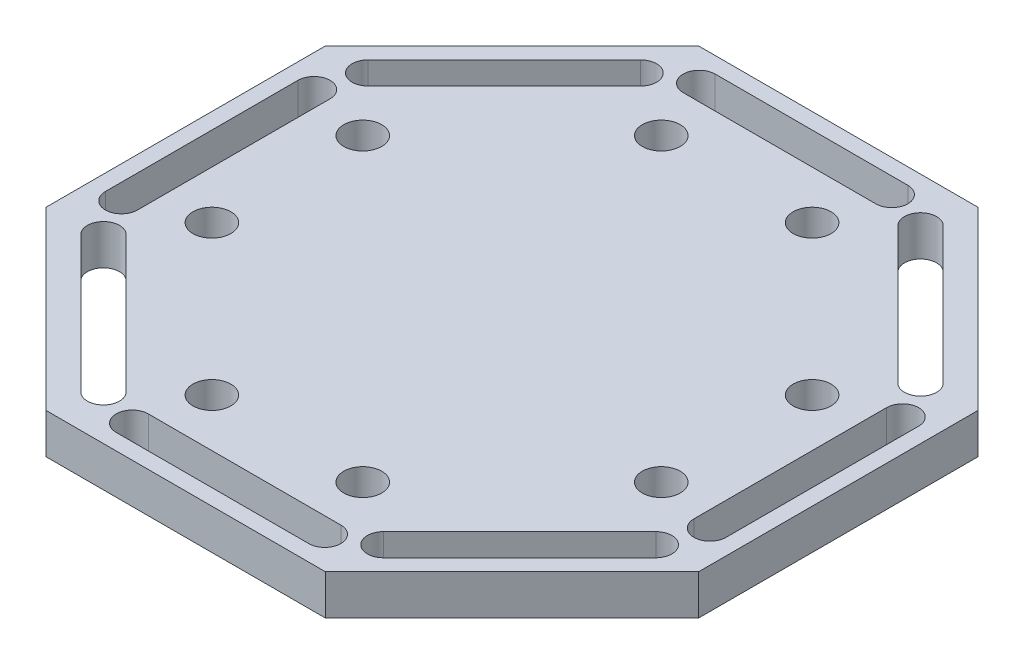
SolidWorks part; units mm, degrees
ref_plane "Front Plane" through (0, 0, 0) normal (0, 0, 1) x (1, 0, 0)
ref_plane "Top Plane" through (0, 0, 0) normal (0, 1, 0) x (1, 0, 0)
ref_plane "Right Plane" through (0, 0, 0) normal (1, 0, 0) x (0, 0, -1)
sketch "Sketch1" plane through (0, 0, 0) normal (0, 1, 0) x (1, 0, 0)
  line L0 (-22.86, -8.0471) -> (-22.86, 7.1929) construction
  line L2 (-25.4, 10.6219) -> (-25.4, -11.4761)
  line L4 (25.4, 11.4761) -> (25.4, -10.6219)
  line L5 (-25.4, 10.6219) -> (25.4, -10.6219) construction
  line L6 (-25.4, -11.4761) -> (25.4, 11.4761) construction
  line L7 (10.6219, -25.4) -> (-11.4761, -25.4)
  line L9 (11.4761, 25.4) -> (-10.6219, 25.4)
  line L11 (10.6219, -25.4) -> (-10.6219, 25.4) construction
  line L12 (11.4761, 25.4) -> (-11.4761, -25.4) construction
  line L13 (-24.13, -8.0471) -> (-24.13, 7.1929)
  line L14 (-25.4, 10.6219) -> (-10.6219, 25.4)
  line L15 (11.4761, 25.4) -> (25.4, 11.4761)
  line L16 (25.4, -10.6219) -> (10.6219, -25.4)
  line L17 (-11.4761, -25.4) -> (-25.4, -11.4761)
  line L18 (-21.59, -8.0471) -> (-21.59, 7.1929)
  line L19 (-20.9566, 9.5763) -> (-10.1803, 20.3526)
  line L20 (-22.7527, 11.3723) -> (-11.9763, 22.1486)
  line L21 (-21.8546, 10.4743) -> (-11.0783, 21.2506) construction
  line L22 (-8.0471, 21.59) -> (7.1929, 21.59)
  line L23 (-8.0471, 24.13) -> (7.1929, 24.13)
  line L24 (-8.0471, 22.86) -> (7.1929, 22.86) construction
  line L25 (9.5763, 20.9566) -> (20.3526, 10.1803)
  line L26 (11.3723, 22.7527) -> (22.1486, 11.9763)
  line L27 (10.4743, 21.8546) -> (21.2506, 11.0783) construction
  line L28 (21.59, 8.0471) -> (21.59, -7.1929)
  line L29 (24.13, 8.0471) -> (24.13, -7.1929)
  line L30 (22.86, 8.0471) -> (22.86, -7.1929) construction
  line L31 (20.9566, -9.5763) -> (10.1803, -20.3526)
  line L32 (22.7527, -11.3723) -> (11.9763, -22.1486)
  line L33 (21.8546, -10.4743) -> (11.0783, -21.2506) construction
  line L34 (8.0471, -21.59) -> (-7.1929, -21.59)
  line L35 (8.0471, -24.13) -> (-7.1929, -24.13)
  line L36 (8.0471, -22.86) -> (-7.1929, -22.86) construction
  line L37 (-9.5763, -20.9566) -> (-20.3526, -10.1803)
  line L38 (-11.3723, -22.7527) -> (-22.1486, -11.9763)
  line L39 (-10.4743, -21.8546) -> (-21.2506, -11.0783) construction
  circle A0 centre (-17.78, 5.969) radius 1.5
  circle A1 centre (-17.78, -5.969) radius 1.5
  circle A2 centre (-5.969, 17.78) radius 1.5
  circle A3 centre (5.969, 17.78) radius 1.5
  circle A4 centre (17.78, 5.969) radius 1.5
  circle A5 centre (17.78, -5.969) radius 1.5
  circle A6 centre (5.969, -17.78) radius 1.5
  circle A7 centre (-5.969, -17.78) radius 1.5
  arc A8 (-24.13, -8.0471) -> (-21.59, -8.0471) centre (-22.86, -8.0471) ccw
  arc A9 (-21.59, 7.1929) -> (-24.13, 7.1929) centre (-22.86, 7.1929) ccw
  arc A10 (-22.7527, 11.3723) -> (-20.9566, 9.5763) centre (-21.8546, 10.4743) ccw
  arc A11 (-10.1803, 20.3526) -> (-11.9763, 22.1486) centre (-11.0783, 21.2506) ccw
  arc A12 (-8.0471, 24.13) -> (-8.0471, 21.59) centre (-8.0471, 22.86) ccw
  arc A13 (7.1929, 21.59) -> (7.1929, 24.13) centre (7.1929, 22.86) ccw
  arc A14 (11.3723, 22.7527) -> (9.5763, 20.9566) centre (10.4743, 21.8546) ccw
  arc A15 (20.3526, 10.1803) -> (22.1486, 11.9763) centre (21.2506, 11.0783) ccw
  arc A16 (24.13, 8.0471) -> (21.59, 8.0471) centre (22.86, 8.0471) ccw
  arc A17 (21.59, -7.1929) -> (24.13, -7.1929) centre (22.86, -7.1929) ccw
  arc A18 (22.7527, -11.3723) -> (20.9566, -9.5763) centre (21.8546, -10.4743) ccw
  arc A19 (10.1803, -20.3526) -> (11.9763, -22.1486) centre (11.0783, -21.2506) ccw
  arc A20 (8.0471, -24.13) -> (8.0471, -21.59) centre (8.0471, -22.86) ccw
  arc A21 (-7.1929, -21.59) -> (-7.1929, -24.13) centre (-7.1929, -22.86) ccw
  arc A22 (-11.3723, -22.7527) -> (-9.5763, -20.9566) centre (-10.4743, -21.8546) ccw
  arc A23 (-20.3526, -10.1803) -> (-22.1486, -11.9763) centre (-21.2506, -11.0783) ccw
  point P0 (0, 0)
  point P6 (0, 0)
  point P15 (-22.86, -0.4271)
  point P30 (0, 0)
  point P35 (-16.4665, 15.8624)
  point P36 (-0.4603, 25.1196)
  point P37 (0, 0)
  point P44 (-0.4271, 22.86)
  point P51 (15.8624, 16.4665)
  point P58 (22.86, 0.4271)
  point P65 (16.4665, -15.8624)
  point P72 (0.4271, -22.86)
  point P79 (-15.8624, -16.4665)
  point P86 (0, 0)
  dimension "D3" = 3
  dimension "D13" = 1.27
  dimension "D1" = 22.098
  dimension "D2" = 17.78
  dimension "D4" = 50.8
  dimension "D5" = 50.8
  dimension "D6" = 5.969
  dimension "D8" = 5.969
  dimension "D9" = 13.9239
  dimension "D10" = 15.24
  dimension "D11" = 3.429
  dimension "D12" = 2.54
  dimension "D7" = 4
  dimension "D14" = 8
extrude "Boss-Extrude1" add sketch "Sketch1" along normal blind 3.175
